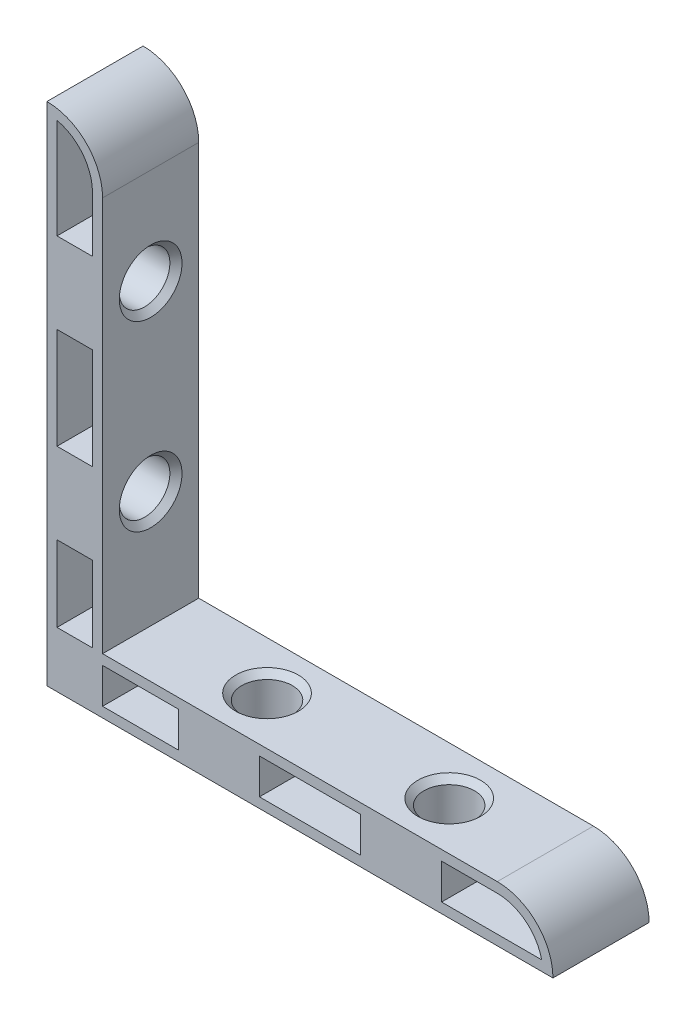
SolidWorks part; units mm, degrees
material "ЦА4М3 ГОСТ 25140-93"
ref_plane "Спереди" through (0, 0, 0) normal (0, 0, 1) x (1, 0, 0)
ref_plane "Сверху" through (0, 0, 0) normal (0, 1, 0) x (1, 0, 0)
ref_plane "Справа" through (0, 0, 0) normal (1, 0, 0) x (0, 0, -1)
sketch "Эскиз1" plane through (0, 0, 0) normal (0, 0, 1) x (1, 0, 0)
  line L0 (0, 50) -> (0, 0)
  line L1 (0, 0) -> (50, 0)
  line L2 (44.5, 5.5) -> (5.5, 5.5)
  line L3 (5.5, 5.5) -> (5.5, 44.5)
  line L4 (1, 48.8875) -> (1, 1)
  line L5 (1, 1) -> (48.8875, 1)
  line L6 (44.5, 4.5) -> (4.5, 4.5)
  line L7 (4.5, 4.5) -> (4.5, 44.5)
  arc A0 (50, 0) -> (44.5, 5.5) centre (44.5, 0) ccw
  arc A1 (5.5, 44.5) -> (0, 50) centre (0, 44.5) ccw
  arc A2 (48.8875, 1) -> (44.5, 4.5) centre (44.5, 0) ccw
  arc A3 (4.5, 44.5) -> (1, 48.8875) centre (0, 44.5) ccw
  point P9 (0, 0)
  dimension "D1" = 50
  dimension "D2" = 5.5
  dimension "D3" = 1
extrude "Бобышка-Вытянуть1" add sketch "Эскиз1" along normal mid plane 9.5
sketch "Эскиз2" plane through (0, 0, 0) normal (0, 0, 1) x (1, 0, 0)
  line L0 (0, 50) -> (0, 0) construction
  line L1 (5.5, 5.5) -> (0, 5.5)
  line L2 (5.5, 5.5) -> (5.5, 0)
  line L3 (5.5, 0) -> (0, 0)
  line L4 (0, 5.5) -> (0, 0)
  line L5 (0, 39) -> (5.5, 39)
  line L6 (0, 39) -> (0, 31)
  line L7 (0, 31) -> (5.5, 31)
  line L8 (5.5, 39) -> (5.5, 31)
  line L9 (5.5, 5.5) -> (5.5, 44.5) construction
  line L10 (0, 0) -> (24.8323, 24.8323) construction
  line L11 (0, 21) -> (5.5, 21)
  line L12 (0, 21) -> (0, 13)
  line L13 (0, 13) -> (5.5, 13)
  line L14 (5.5, 21) -> (5.5, 13)
  line L15 (21, 5.5) -> (13, 5.5)
  line L16 (13, 0) -> (13, 5.5)
  line L17 (21, 0) -> (13, 0)
  line L18 (21, 0) -> (21, 5.5)
  line L19 (39, 5.5) -> (31, 5.5)
  line L20 (31, 0) -> (31, 5.5)
  line L21 (39, 0) -> (31, 0)
  line L22 (39, 0) -> (39, 5.5)
  point P18 (0, 35)
  point P20 (0, 17)
  dimension "D1" = 15
  dimension "D2" = 8
  dimension "D3" = 18
extrude "Бобышка-Вытянуть2" add sketch "Эскиз2" along normal up to surface and the other way up to surface
sketch "Эскиз3" plane through (0, 0, 0) normal (0, 0, 1) x (1, 0, 0)
  line L4 (0, 0) -> (50, 0)
  line L5 (44.5, 5.5) -> (5.5, 5.5)
  line L6 (5.5, 5.5) -> (5.5, 44.5)
  line L7 (0, 50) -> (0, 0)
  line L8 (0, 0) -> (50, 0)
  line L9 (44.5, 5.5) -> (5.5, 5.5)
  line L10 (5.5, 5.5) -> (5.5, 44.5)
  line L11 (0, 50) -> (0, 0)
  arc A2 (50, 0) -> (44.5, 5.5) centre (44.5, 0) ccw
  arc A3 (5.5, 44.5) -> (0, 50) centre (0, 44.5) ccw
  arc A4 (50, 0) -> (44.5, 5.5) centre (44.5, 0) ccw
  arc A5 (5.5, 44.5) -> (0, 50) centre (0, 44.5) ccw
  dimension "D1" = 0
extrude "Бобышка-Вытянуть3" add sketch "Эскиз3" along normal mid plane 2
hole_wizard "Отверстие обработанное метчиком M61" positions "Эскиз4" profile "Эскиз5" tap size "M6" standard "ISO" end condition through all
sketch "Эскиз4" plane through (0, 0, 0) normal (-1, 0, 0) x (0, 0, 1)
  line L0 (4.75, 39) -> (4.75, 31)
  line L1 (4.75, 50) -> (4.75, 0) construction
  line L3 (1, 39) -> (4.75, 39) construction
  line L4 (4.75, 31) -> (1, 31) construction
  line L5 (4.75, 21) -> (4.75, 13)
  line L7 (1, 21) -> (4.75, 21) construction
  line L8 (4.75, 13) -> (1, 13) construction
  point P0 (0, 35)
  point P2 (0, 17)
  point P20 (4.75, 35)
  point P25 (0, 0)
  point P28 (0, 0)
  point P31 (4.75, 17)
  point P32 (-1.1124, 17)
  point P34 (0, 0)
sketch "Эскиз5" plane through (0, 35, 0) normal (0, 1, 0) x (0, 0, 1)
  line L0 (0, 0) -> (0, 5.5)
  line L1 (0, 5.5) -> (3.1, 5.5)
  line L2 (2.5, 4.9) -> (2.5, 0.6)
  line L3 (2.5, 0.6) -> (3.1, 0)
  line L5 (3.1, 0) -> (0, 0)
  line L6 (-2.5, 0.6) -> (-3.1, 0) construction
  line L7 (3.1, 5.5) -> (2.5, 4.9)
  line L8 (-3.1, 5.5) -> (-2.5, 4.9) construction
  line L11 (0, -6.35) -> (0, 107.95) construction
  dimension "Диаметр проходного сверла" = 5
  dimension "Глубина проходного сверла" = 5.5
  dimension "Диаметр передней зенковки" = 6.2
  dimension "Угол передней зенковки" = 90
  dimension "Диаметр задней зенковки" = 6.2
  dimension "Угол задней зенковки" = 90
cosmetic thread "Отверстие резьбы1" parameters "D2"=6
cosmetic thread "Отверстие резьбы2" parameters "D2"=6
ref_plane "Плоскость1" through (0, 0, 0) normal (-0.7071, 0.7071, 0) x (0.7071, 0.7071, 0)
mirror "Зеркальное отражение1" about plane through (0, 0, 0) normal (-0.7071, 0.7071, 0) of "Отверстие обработанное метчиком M61"
